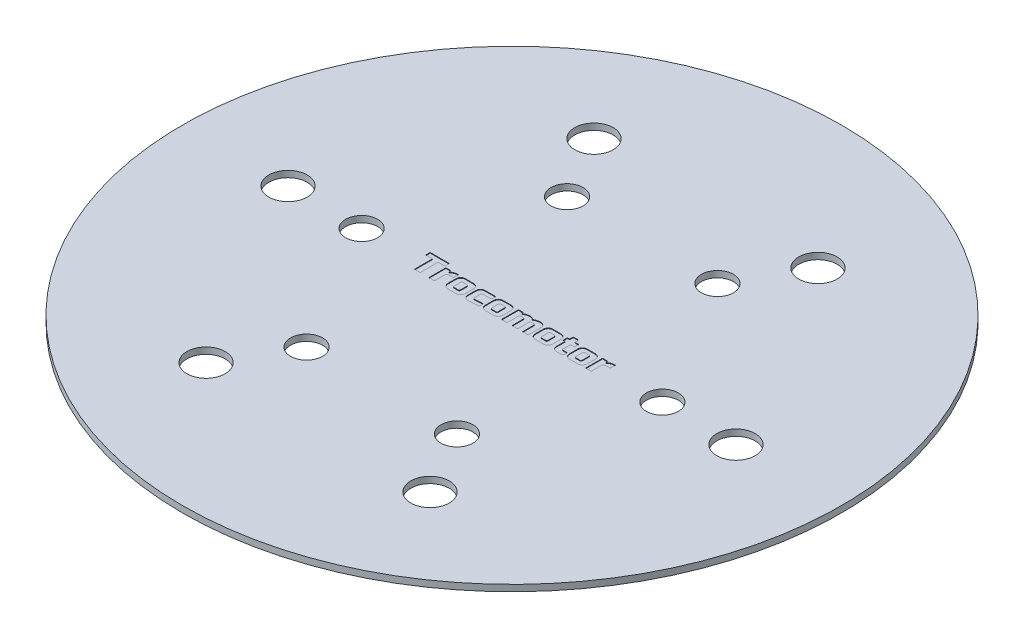
SolidWorks part; units mm, degrees
ref_plane "前视基准面" through (0, 0, 0) normal (0, 0, 1) x (1, 0, 0)
ref_plane "上视基准面" through (0, 0, 0) normal (0, 1, 0) x (1, 0, 0)
ref_plane "右视基准面" through (0, 0, 0) normal (1, 0, 0) x (0, 0, -1)
sketch "Sketch1" plane through (0, 0, 0) normal (0, 1, 0) x (1, 0, 0)
  circle A0 centre (0, 0) radius 23.5 construction
  circle A1 centre (0, 0) radius 51.5
  circle A2 centre (0, 0) radius 35 construction
  circle A3 centre (23.5, 0) radius 2.5
  circle A4 centre (35, 0) radius 3
  circle A5 centre (11.75, -20.3516) radius 2.5
  circle A6 centre (17.5, -30.3109) radius 3
  circle A7 centre (-11.75, -20.3516) radius 2.5
  circle A8 centre (-17.5, -30.3109) radius 3
  circle A9 centre (-23.5, 0) radius 2.5
  circle A10 centre (-35, 0) radius 3
  circle A11 centre (-11.75, 20.3516) radius 2.5
  circle A12 centre (-17.5, 30.3109) radius 3
  circle A13 centre (11.75, 20.3516) radius 2.5
  circle A14 centre (17.5, 30.3109) radius 3
  point P31 (0, 0)
  dimension "D1" = 103
  dimension "D2" = 6
  dimension "22.5*2" = 47
  dimension "D3" = 70
  dimension "D4" = 6
  dimension "D5" = 5
extrude "Boss-Extrude1" add sketch "Sketch1" along normal blind 1
sketch "Sketch2" plane through (0, 1, 0) normal (0, 1, 0) x (1, 0, 0)
  line L0 (-16.0211, -1.3857) -> (16.0211, -1.3857) construction
  text T0 "Trocomotor" font "Russo One" height 3.5
  point P0 (16.0211, 0)
  point P4 (0, 0)
extrude "Cut-Extrude1" cut sketch "Sketch2" against normal blind 0.1
